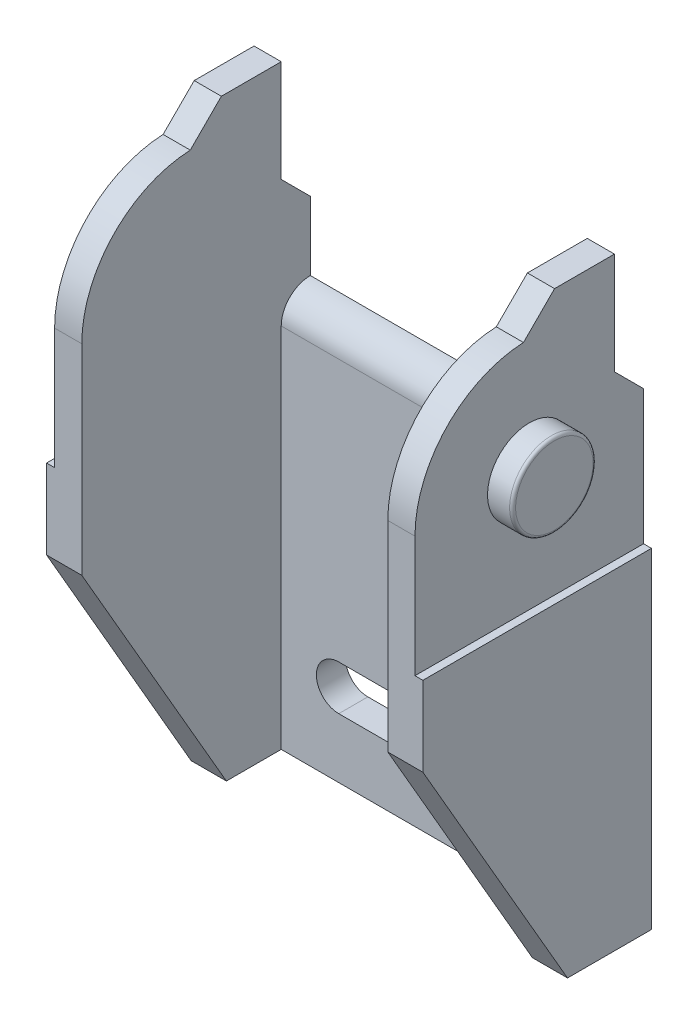
SolidWorks part; units mm, degrees
ref_plane "Front Plane" through (0, 0, 0) normal (0, 0, 1) x (1, 0, 0)
ref_plane "Top Plane" through (0, 0, 0) normal (0, 1, 0) x (1, 0, 0)
ref_plane "Right Plane" through (0, 0, 0) normal (1, 0, 0) x (0, 0, -1)
ref_plane "Plane1" through (-13.92, 0, 0) normal (-1, 0, 0) x (0, -1, 0)
sketch "Sketch1" plane through (-13.92, 0, 0) normal (-1, 0, 0) x (0, -1, 0)
  line L0 (19.9475, 5.6221) -> (3.1675, 15.31)
  line L1 (3.1675, 15.31) -> (3.1675, 5.6221)
  line L2 (3.1675, 5.6221) -> (19.9475, 5.6221)
extrude "Boss-Extrude1" add sketch "Sketch1" against normal blind 3.67
sketch "Sketch2" plane through (0, -3.1675, 0) normal (0, 1, 0) x (-1, 0, 0)
  line L0 (10.25, 5.6221) -> (10.25, 15.31)
  line L1 (10.25, 15.31) -> (13.92, 15.31)
  line L2 (13.92, 15.31) -> (13.92, 5.6221)
  line L3 (13.92, 5.6221) -> (10.25, 5.6221)
extrude "Boss-Extrude2" add sketch "Sketch2" along normal blind 9.735
sketch "Sketch3" plane through (0, 0, 5.6221) normal (0, 0, -1) x (-1, 0, 0)
  line L0 (10.25, 6.5675) -> (13.92, 6.5675)
  line L1 (13.92, 6.5675) -> (13.92, -19.9475)
  line L2 (13.92, -19.9475) -> (10.25, -19.9475)
  line L3 (10.25, -19.9475) -> (10.25, 6.5675)
extrude "Boss-Extrude3" add sketch "Sketch3" along normal blind 5.6221
sketch "Sketch4" plane through (-10.25, 0, 0) normal (1, 0, 0) x (0, 0, -1)
  line L0 (0, -19.9475) -> (-1.95, -19.9475)
  line L1 (-1.95, -19.9475) -> (-1.95, 4.6175)
  line L2 (0, 6.5675) -> (0, -19.9475)
  arc A0 (-1.95, 4.6175) -> (0, 6.5675) centre (0, 4.6175) cw
extrude "Boss-Extrude4" add sketch "Sketch4" along normal blind 20.5
sketch "Sketch5" plane through (0, 6.5675, 0) normal (0, 1, 0) x (-1, 0, 0)
  line L0 (10.25, 0) -> (10.25, 15.31)
  line L1 (10.25, 15.31) -> (13.92, 15.31)
  line L2 (13.92, 15.31) -> (13.92, 0)
  line L3 (13.92, 0) -> (10.25, 0)
extrude "Boss-Extrude5" add sketch "Sketch5" along normal blind 13.38
sketch "Sketch6" plane through (10.25, 0, 0) normal (1, 0, 0) x (0, 0, -1)
  line L0 (-15.31, -3.1675) -> (-15.31, 19.9475)
  line L1 (-15.31, 19.9475) -> (0, 19.9475)
  line L2 (0, 19.9475) -> (0, -19.9475)
  line L3 (0, -19.9475) -> (-5.6221, -19.9475)
  line L4 (-5.6221, -19.9475) -> (-15.31, -3.1675)
extrude "Boss-Extrude6" add sketch "Sketch6" along normal blind 2.35
sketch "Sketch7" plane through (0, 0, 15.31) normal (0, 0, 1) x (1, 0, 0)
  line L0 (12.07, 19.9475) -> (12.07, 2.1675)
  line L1 (12.07, 2.1675) -> (13.92, 2.1675)
  line L2 (13.92, 2.1675) -> (13.92, 19.9475)
  line L3 (13.92, 19.9475) -> (12.07, 19.9475)
extrude "Cut-Extrude1" cut sketch "Sketch7" against normal through all
sketch "Sketch8" plane through (12.07, 0, 0) normal (1, 0, 0) x (0, 0, -1)
  line L0 (-8.0431, 17.8642) -> (-5.9598, 19.9475)
  line L1 (-5.9598, 19.9475) -> (-15.31, 19.9475)
  line L2 (-15.31, 19.9475) -> (-15.31, 10.263)
  arc A0 (-15.31, 10.263) -> (-8.0431, 17.8642) centre (-7.7011, 10.263) cw
extrude "Cut-Extrude2" cut sketch "Sketch8" against normal up to next
sketch "Sketch9" plane through (0, 0, 15.31) normal (0, 0, 1) x (1, 0, 0)
  line L0 (-13.92, 2.1675) -> (-12.07, 2.1675)
  line L1 (-12.07, 2.1675) -> (-12.07, 19.9475)
  line L2 (-12.07, 19.9475) -> (-13.92, 19.9475)
  line L3 (-13.92, 19.9475) -> (-13.92, 2.1675)
extrude "Cut-Extrude3" cut sketch "Sketch9" against normal through all
sketch "Sketch10" plane through (-12.07, 0, 0) normal (-1, 0, 0) x (0, 0, 1)
  line L0 (1.95, 13.1175) -> (1.95, 19.9475)
  line L1 (1.95, 19.9475) -> (0, 19.9475)
  line L2 (0, 19.9475) -> (0, 11.1675)
  line L3 (0, 11.1675) -> (1.95, 13.1175)
extrude "Cut-Extrude4" cut sketch "Sketch10" against normal up to next
sketch "Sketch11" plane through (-12.07, 0, 0) normal (-1, 0, 0) x (0, 0, 1)
  line L0 (5.9598, 19.9475) -> (8.0431, 17.8642)
  line L1 (15.31, 10.263) -> (15.31, 19.9475)
  line L2 (15.31, 19.9475) -> (5.9598, 19.9475)
  arc A0 (8.0431, 17.8642) -> (15.31, 10.263) centre (7.7011, 10.263) cw
extrude "Cut-Extrude5" cut sketch "Sketch11" against normal up to next
sketch "Sketch12" plane through (12.07, 0, 0) normal (1, 0, 0) x (0, 0, -1)
  line L0 (-1.95, 19.9475) -> (-1.95, 13.1175)
  line L1 (-1.95, 13.1175) -> (0, 11.1675)
  line L2 (0, 11.1675) -> (0, 19.9475)
  line L3 (0, 19.9475) -> (-1.95, 19.9475)
extrude "Cut-Extrude6" cut sketch "Sketch12" against normal through all
sketch "Sketch13" plane through (0, 0, 1.95) normal (0, 0, 1) x (1, 0, 0)
  line L0 (-4.25, -19.9475) -> (-4.25, -14.4475) construction
  line L1 (-6.3955, -14.4475) -> (-2.1045, -14.4475) construction
  line L2 (0, 4.6175) -> (0, -19.9475) construction
  line L3 (10.25, -19.9475) -> (-10.25, -19.9475) construction
  line L4 (-6.3955, -12.9475) -> (-2.1045, -12.9475)
  line L5 (10.25, 4.6175) -> (-10.25, 4.6175) construction
  line L6 (-6.3955, -15.9475) -> (-2.1045, -15.9475)
  line L7 (4.25, -19.9475) -> (4.25, -10.4475) construction
  line L8 (2.1045, -10.4475) -> (6.3955, -10.4475) construction
  line L9 (2.1045, -8.9475) -> (6.3955, -8.9475)
  line L10 (2.1045, -11.9475) -> (6.3955, -11.9475)
  line L11 (-4.25, -14.4475) -> (-10.25, -14.4475) construction
  line L12 (-10.25, 4.6175) -> (-10.25, -19.9475) construction
  line L13 (4.25, -10.4475) -> (10.25, -10.4475) construction
  line L14 (10.25, 4.6175) -> (10.25, -19.9475) construction
  arc A0 (-6.3955, -12.9475) -> (-6.3955, -15.9475) centre (-6.3955, -14.4475) ccw
  arc A1 (-2.1045, -15.9475) -> (-2.1045, -12.9475) centre (-2.1045, -14.4475) ccw
  arc A2 (2.1045, -8.9475) -> (2.1045, -11.9475) centre (2.1045, -10.4475) ccw
  arc A3 (6.3955, -11.9475) -> (6.3955, -8.9475) centre (6.3955, -10.4475) ccw
  point P3 (-4.25, -14.4475)
  point P19 (4.25, -10.4475)
  dimension "D3" = 1.5
  dimension "D1" = 5.5
  dimension "D2" = 9.5
  dimension "D4" = 6
  dimension "D5" = 6
extrude "Cut-Extrude7" cut sketch "Sketch13" against normal through all
ref_plane "Plane2" through (0, 0, 7.655) normal (0, 0, 1) x (1, 0, 0)
sketch "Sketch15" plane through (0, 0, 7.655) normal (0, 0, 1) x (1, 0, 0)
  line L0 (12.07, 13.0075) -> (12.07, 10.2125)
  line L1 (12.07, 10.2125) -> (13.75, 10.2125)
  line L2 (13.75, 10.2125) -> (13.75, 13.0075)
  line L3 (13.75, 13.0075) -> (12.07, 13.0075)
  line L4 (12.07, 10.2125) -> (13.75, 10.2125) construction
revolve "Revolve1" add sketch "Sketch15" angle 360 about L4
sketch "Sketch16" plane through (0, 0, 7.655) normal (0, 0, 1) x (1, 0, 0)
  line L0 (-13.75, 13.0075) -> (-13.75, 10.2125)
  line L1 (-13.75, 10.2125) -> (-12.07, 10.2125)
  line L2 (-12.07, 10.2125) -> (-12.07, 13.0075)
  line L3 (-12.07, 13.0075) -> (-13.75, 13.0075)
  line L4 (-13.75, 10.2125) -> (-12.07, 10.2125) construction
revolve "Revolve2" add sketch "Sketch16" angle 360 about L4
fillet "Fillet1" radius 0.2 2 edges at (-13.75, 10.2125, 4.86) (13.75, 10.2125, 4.86)
ref_plane "Plane3" through (-13.92, -19.9475, 5.6221) normal (-1, 0, 0) x (0, 0, 1)
sketch "Sketch17" plane through (-13.92, -19.9475, 5.6221) normal (-1, 0, 0) x (0, 0, 1)
  line L0 (9.6879, 22.115) -> (-5.6221, 22.115)
  line L1 (-5.6221, 22.115) -> (-5.6221, 0)
  line L2 (-5.6221, 0) -> (0, 0)
  line L3 (0, 0) -> (9.6879, 16.78)
  line L4 (9.6879, 16.78) -> (9.6879, 22.115)
extrude "Cut-Extrude8" cut sketch "Sketch17" against normal blind 1.31
